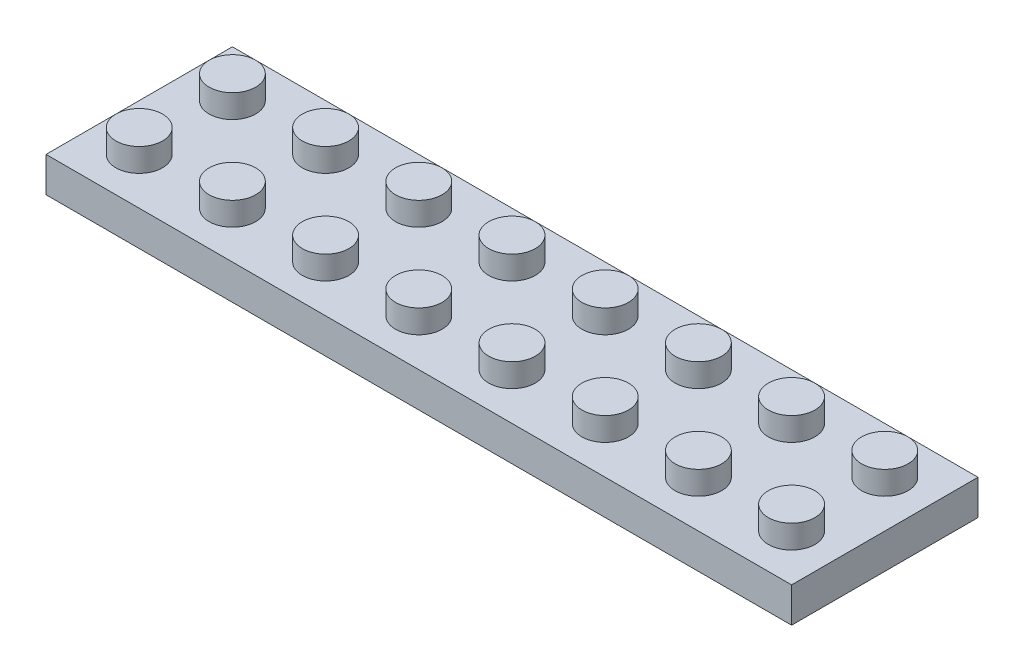
SolidWorks part; units mm, degrees
ref_plane "Front Plane" through (0, 0, 0) normal (0, 0, 1) x (1, 0, 0)
ref_plane "Top Plane" through (0, 0, 0) normal (0, 1, 0) x (1, 0, 0)
ref_plane "Right Plane" through (0, 0, 0) normal (1, 0, 0) x (0, 0, -1)
sketch "Sketch1" plane through (0, 0, 0) normal (0, 1, 0) x (1, 0, 0)
  line L1 (32, -8) -> (-32, -8)
  line L2 (32, -8) -> (32, 8)
  line L3 (32, 8) -> (-32, 8)
  line L4 (-32, -8) -> (-32, 8)
  line L5 (32, -8) -> (-32, 8) construction
  line L6 (32, 8) -> (-32, -8) construction
  point P0 (0, 0)
  dimension "D1" = 64
  dimension "D2" = 16
extrude "Boss-Extrude1" add sketch "Sketch1" along normal blind 3
sketch "Sketch2" plane through (0, 3, 0) normal (0, 1, 0) x (1, 0, 0)
  line L0 (-32, 8) -> (-32, -8) construction
  line L1 (32, 8) -> (-32, 8) construction
  circle A0 centre (-28, 4) radius 2
  circle A1 centre (-20, 4) radius 2
  circle A2 centre (-12, 4) radius 2
  circle A3 centre (-4, 4) radius 2
  circle A4 centre (4, 4) radius 2
  circle A5 centre (12, 4) radius 2
  circle A6 centre (20, 4) radius 2
  circle A7 centre (28, 4) radius 2
  circle A8 centre (-20, -4) radius 2
  circle A9 centre (-12, -4) radius 2
  circle A10 centre (-4, -4) radius 2
  circle A11 centre (4, -4) radius 2
  circle A12 centre (12, -4) radius 2
  circle A13 centre (20, -4) radius 2
  circle A14 centre (28, -4) radius 2
  circle A15 centre (-28, -4) radius 2
  dimension "D1" = 4
  dimension "D2" = 4
  dimension "D3" = 4
  dimension "D4" = 8
  dimension "D5" = 2
extrude "Boss-Extrude2" add sketch "Sketch2" along normal blind 2
shell "Shell1" thickness 1
sketch "Sketch3" plane through (0, 2, 0) normal (0, -1, 0) x (1, 0, 0)
  line L0 (-32, -8) -> (-32, 8) construction
  line L1 (-32, 8) -> (32, 8) construction
  circle A0 centre (-24, 0) radius 2.8
  circle A1 centre (-24, 0) radius 1.8
  dimension "D3" = 5.6
  dimension "D4" = 3.6
  dimension "D1" = 8
  dimension "D2" = 8
extrude "Boss-Extrude3" add sketch "Sketch3" along normal up to surface (2 mm away) up to face at (0, 0, 0)
pattern_linear "LPattern1" count 7 spacing 8 along (1, 0, 0) of "Boss-Extrude3"
